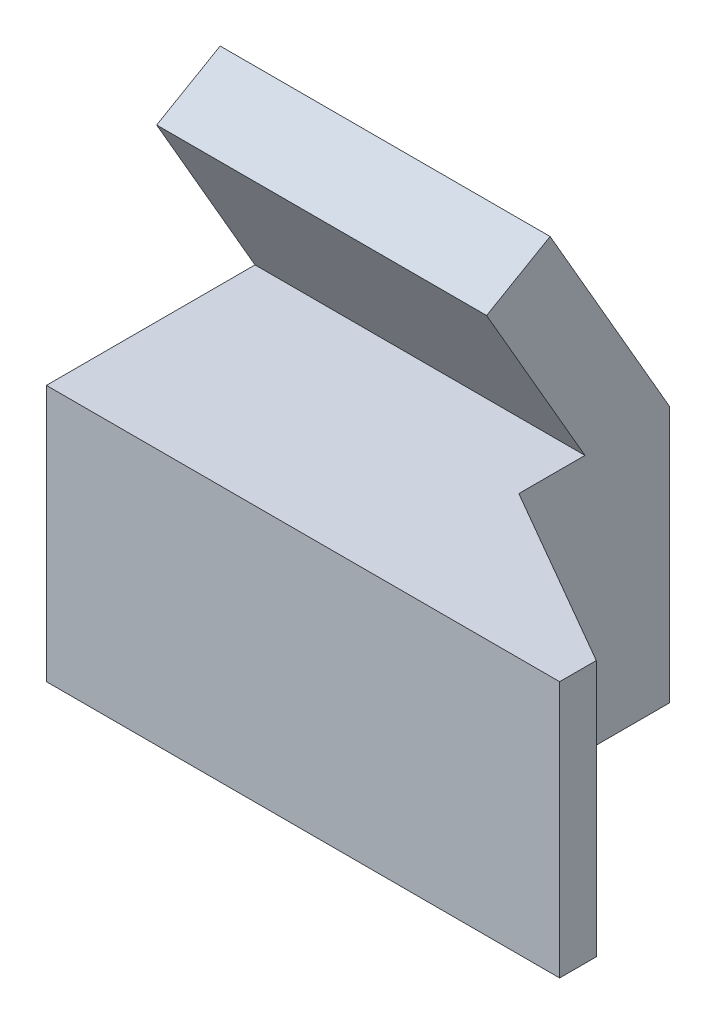
SolidWorks part; units mm, degrees
ref_plane "Front Plane" through (0, 0, 0) normal (0, 0, 1) x (1, 0, 0)
ref_plane "Top Plane" through (0, 0, 0) normal (0, 1, 0) x (1, 0, 0)
ref_plane "Right Plane" through (0, 0, 0) normal (1, 0, 0) x (0, 0, -1)
sketch "Sketch1" plane through (0, 0, 0) normal (0, 1, 0) x (1, 0, 0)
  line L0 (57.15, 0) -> (88.9, 0)
  line L1 (0, 0) -> (57.15, 0)
  line L2 (0, 0) -> (0, 50.8)
  line L3 (0, 50.8) -> (57.15, 50.8)
  line L4 (57.15, 24.6809) -> (57.15, 50.8)
  line L5 (88.9, 0) -> (88.9, 6.35)
  line L6 (88.9, 6.35) -> (57.15, 24.6809)
  dimension "D1" = 50.8
  dimension "D2" = 57.15
  dimension "D3" = 31.75
  dimension "D4" = 6.35
  dimension "D5" = 60
  dimension "D6" = 57.15
extrude "Boss-Extrude1" add sketch "Sketch1" along normal blind 44.45
sketch "Sketch3" plane through (24.9746, 0, -43.2573) normal (0.5, 0, -0.866) x (-0.866, 0, -0.5)
  line L0 (-73.8147, 0) -> (-37.1529, 0) construction
  line L1 (-73.8147, 44.45) -> (-73.8147, 0) construction
  circle A0 centre (-54.7647, 22.352) radius 9.525
  dimension "D1" = 22.352
  dimension "D3" = 19.05
  dimension "D2" = 19.05
extrude "Cut-Extrude1" cut sketch "Sketch3" against normal blind 6.35
sketch "Sketch4" plane through (0, 0, 0) normal (-1, 0, 0) x (0, 0, 1)
  line L0 (-50.8, 44.45) -> (-30.099, 80.3052)
  line L2 (-19.1005, 73.9552) -> (-36.1353, 44.45)
  line L3 (-50.8, 44.45) -> (0, 44.45) construction
  line L4 (-50.8, 44.45) -> (-50.8, 0) construction
  line L5 (-30.099, 80.3052) -> (-19.1005, 73.9552)
  line L9 (-50.8, 0) -> (0, 0)
  line L10 (0, 0) -> (0, 44.45)
  line L11 (0, 44.45) -> (-50.8, 44.45)
  line L12 (-50.8, 44.45) -> (-50.8, 0)
  line L13 (-50.8, 0) -> (0, 0)
  line L14 (0, 0) -> (0, 44.45)
  line L15 (0, 44.45) -> (-36.1353, 44.45)
  line L16 (-50.8, 44.45) -> (-50.8, 0)
  dimension "D1" = 30
  dimension "D2" = 12.7
  dimension "D3" = 41.402
  dimension "D4" = 60
  dimension "D5" = 0
extrude "Boss-Extrude2" add sketch "Sketch4" against normal blind 57.15
sketch "Sketch5" plane through (0, 33.1095, -57.3474) normal (0, 0.5, -0.866) x (-1, 0, 0)
  line L0 (-57.15, 13.0948) -> (0, 13.0948) construction
  line L1 (0, 54.4968) -> (0, 13.0948) construction
  circle A0 centre (-28.702, 35.4468) radius 9.525
  point P6 (-45.1206, 62.7342)
  dimension "D3" = 19.05
  dimension "D1" = 22.352
  dimension "D2" = 28.702
extrude "Cut-Extrude2" cut sketch "Sketch5" against normal blind 6.35
sketch "Sketch6" plane through (0, 0, -50.8) normal (0, 0, -1) x (-1, 0, 0)
  line L0 (-57.15, 44.45) -> (-57.15, 0) construction
  line L1 (-57.15, 44.45) -> (0, 44.45) construction
  line L2 (0, 44.45) -> (0, 0) construction
  line L3 (-57.15, 0) -> (0, 0) construction
  circle A0 centre (-41.148, 31.75) radius 4.7625
  circle A1 centre (-16.002, 31.75) radius 4.7625
  circle A2 centre (-16.002, 12.7) radius 4.7625
  circle A3 centre (-41.148, 12.7) radius 4.7625
  dimension "D1" = 9.525
  dimension "D6" = 16.002
  dimension "D7" = 12.7
  dimension "D2" = 16.002
  dimension "D3" = 12.7
  dimension "D8" = 19.05
  dimension "D4" = 2
  dimension "D5" = 2
extrude "Cut-Extrude3" cut sketch "Sketch6" against normal blind 12.7
